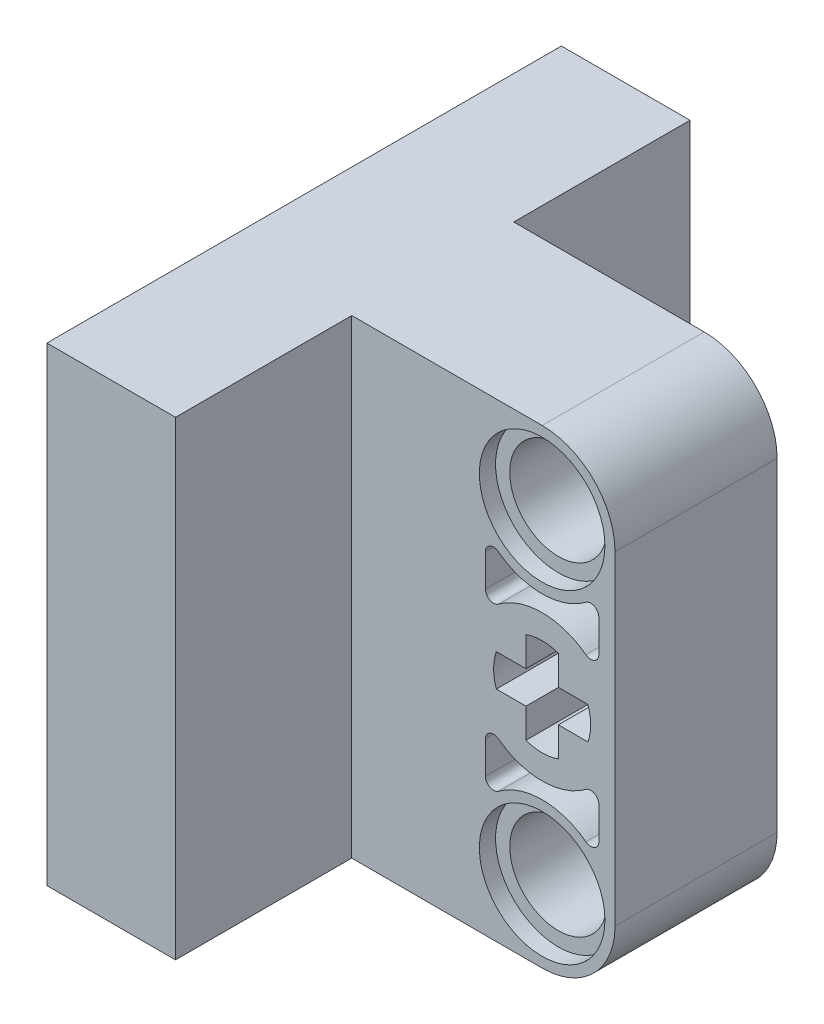
SolidWorks part; units mm, degrees
ref_plane "Front Plane" through (0, 0, 0) normal (0, 0, 1) x (1, 0, 0)
ref_plane "Top Plane" through (0, 0, 0) normal (0, 1, 0) x (1, 0, 0)
ref_plane "Right Plane" through (0, 0, 0) normal (1, 0, 0) x (0, 0, -1)
ref_plane "Plane1" through (0, 0, 4) normal (0, 0, 1) x (1, 0, 0)
sketch "Sketch1" plane through (0, 0, 4) normal (0, 0, 1) x (1, 0, 0)
  line L0 (-3.6, 0) -> (-3.6, -16)
  line L1 (3.6, -16) -> (3.6, 0)
  arc A0 (3.6, 0) -> (-3.6, 0) centre (0, 0) ccw
  arc A1 (-3.6, -16) -> (3.6, -16) centre (0, -16) ccw
  dimension "D1" = 7.2
  dimension "D2" = 16
extrude "Boss-Extrude1" add sketch "Sketch1" against normal blind 8
ref_plane "Plane6" through (0, 0, 0) normal (-1, 0, 0) x (0, 0, 1)
sketch "Sketch15" plane through (0, 0, 0) normal (-1, 0, 0) x (0, 0, 1)
  line L1 (-4, 3.6) -> (4, 3.6)
  line L2 (-4, 3.6) -> (-4, -19.6)
  line L3 (-4, -19.6) -> (4, -19.6)
  line L4 (4, 3.6) -> (4, -19.6)
extrude "Boss-Extrude2" add sketch "Sketch15" along normal blind 15.75
sketch "Sketch3" plane through (0, 0, 4) normal (0, 0, 1) x (1, 0, 0)
  line L0 (2.8, -4.8) -> (2.8, -3.2)
  line L1 (-2.8, -3.2) -> (-2.8, -4.8)
  arc A0 (2.8, -3.2) -> (2.16, -2.88) centre (2.4, -3.2) ccw
  arc A1 (2.16, -2.88) -> (-2.16, -2.88) centre (0, 0) cw
  arc A2 (-2.16, -2.88) -> (-2.8, -3.2) centre (-2.4, -3.2) ccw
  arc A3 (-2.8, -4.8) -> (-2.16, -5.12) centre (-2.4, -4.8) ccw
  arc A4 (-2.16, -5.12) -> (2.16, -5.12) centre (0, -8) cw
  arc A5 (2.16, -5.12) -> (2.8, -4.8) centre (2.4, -4.8) ccw
extrude "Cut-Extrude2" cut sketch "Sketch3" against normal blind 3.1
sketch "Sketch5" plane through (0, 0, 4) normal (0, 0, 1) x (1, 0, 0)
  line L0 (2.8, -12.8) -> (2.8, -11.2)
  line L1 (-2.8, -11.2) -> (-2.8, -12.8)
  arc A0 (2.8, -11.2) -> (2.16, -10.88) centre (2.4, -11.2) ccw
  arc A1 (2.16, -10.88) -> (-2.16, -10.88) centre (0, -8) cw
  arc A2 (-2.16, -10.88) -> (-2.8, -11.2) centre (-2.4, -11.2) ccw
  arc A3 (-2.8, -12.8) -> (-2.16, -13.12) centre (-2.4, -12.8) ccw
  arc A4 (-2.16, -13.12) -> (2.16, -13.12) centre (0, -16) cw
  arc A5 (2.16, -13.12) -> (2.8, -12.8) centre (2.4, -12.8) ccw
extrude "Cut-Extrude4" cut sketch "Sketch5" against normal blind 3.1
sketch "Sketch7" plane through (0, 0, -4) normal (0, 0, -1) x (-1, 0, 0)
  line L0 (2.8, -4.8) -> (2.8, -3.2)
  line L1 (-2.8, -3.2) -> (-2.8, -4.8)
  arc A0 (2.8, -3.2) -> (2.16, -2.88) centre (2.4, -3.2) ccw
  arc A1 (2.16, -2.88) -> (-2.16, -2.88) centre (0, 0) cw
  arc A2 (-2.16, -2.88) -> (-2.8, -3.2) centre (-2.4, -3.2) ccw
  arc A3 (-2.8, -4.8) -> (-2.16, -5.12) centre (-2.4, -4.8) ccw
  arc A4 (-2.16, -5.12) -> (2.16, -5.12) centre (0, -8) cw
  arc A5 (2.16, -5.12) -> (2.8, -4.8) centre (2.4, -4.8) ccw
extrude "Cut-Extrude6" cut sketch "Sketch7" against normal blind 3.1
sketch "Sketch8" plane through (0, 0, -4) normal (0, 0, -1) x (-1, 0, 0)
  line L0 (-2.8, -11.2) -> (-2.8, -12.8)
  line L1 (2.8, -12.8) -> (2.8, -11.2)
  arc A0 (2.16, -10.88) -> (-2.16, -10.88) centre (0, -8) cw
  arc A1 (-2.16, -10.88) -> (-2.8, -11.2) centre (-2.4, -11.2) ccw
  arc A2 (-2.8, -12.8) -> (-2.16, -13.12) centre (-2.4, -12.8) ccw
  arc A3 (-2.16, -13.12) -> (2.16, -13.12) centre (0, -16) cw
  arc A4 (2.16, -13.12) -> (2.8, -12.8) centre (2.4, -12.8) ccw
  arc A5 (2.8, -11.2) -> (2.16, -10.88) centre (2.4, -11.2) ccw
extrude "Cut-Extrude7" cut sketch "Sketch8" against normal blind 3.1
ref_plane "Plane2" through (0, -16, 0) normal (0, 1, 0) x (1, 0, 0)
sketch "Sketch10" plane through (0, -16, 0) normal (0, 1, 0) x (1, 0, 0)
  line L0 (3.1, 4) -> (0, 4)
  line L1 (0, 4) -> (0, -4)
  line L2 (0, -4) -> (3.1, -4)
  line L3 (3.1, -4) -> (3.1, -3.2)
  line L4 (3.1, -3.2) -> (2.4, -3.2)
  line L5 (2.4, -3.2) -> (2.4, 3.2)
  line L6 (2.4, 3.2) -> (3.1, 3.2)
  line L7 (3.1, 3.2) -> (3.1, 4)
  line L8 (0, 4) -> (0, -4) construction
revolve "Cut-Revolve1" cut sketch "Sketch10" angle 360 about L8
ref_plane "Plane3" through (0, 16, 0) normal (0, 1, 0) x (1, 0, 0)
ref_plane "Plane4" through (0, -8, 0) normal (0, 1, 0) x (1, 0, 0)
sketch "Sketch12" plane through (0, -8, 0) normal (0, 1, 0) x (1, 0, 0)
  line L0 (3.1, 4) -> (0, 4)
  line L1 (0, 4) -> (0, -4)
  line L2 (0, -4) -> (3.1, -4)
  line L3 (3.1, -4) -> (3.1, -3.2)
  line L4 (3.1, -3.2) -> (2.4, -3.2)
  line L5 (2.4, -3.2) -> (2.4, 3.2)
  line L6 (2.4, 3.2) -> (3.1, 3.2)
  line L7 (3.1, 3.2) -> (3.1, 4)
  line L8 (0, 4) -> (0, -4) construction
sketch "Sketch13" plane through (0, 0, 0) normal (0, 1, 0) x (1, 0, 0)
  line L0 (3.1, 4) -> (0, 4)
  line L1 (0, 4) -> (0, -4)
  line L2 (0, -4) -> (3.1, -4)
  line L3 (3.1, -4) -> (3.1, -3.2)
  line L4 (3.1, -3.2) -> (2.4, -3.2)
  line L5 (2.4, -3.2) -> (2.4, 3.2)
  line L6 (2.4, 3.2) -> (3.1, 3.2)
  line L7 (3.1, 3.2) -> (3.1, 4)
  line L8 (0, 4) -> (0, -4) construction
revolve "Cut-Revolve4" cut sketch "Sketch13" angle 360 about L8
ref_plane "Plane5" through (0, 8, 0) normal (0, 1, 0) x (1, 0, 0)
sketch "Sketch14" plane through (0, 0, 4) normal (0, 0, 1) x (1, 0, 0)
  line L0 (-3.6, -8) -> (-2.26, -8) construction
  line L2 (-2.26, -8) -> (-2.26, -7.2) construction
  line L3 (-2.26, -8) -> (-2.26, -8.8) construction
  line L4 (-2.26, -7.2) -> (-0.8, -7.2)
  line L5 (-0.8, -7.2) -> (-0.8, -5.74)
  line L6 (-0.8, -5.74) -> (0.8, -5.74) construction
  line L7 (0.8, -5.74) -> (0.8, -7.2)
  line L8 (0.8, -7.2) -> (2.26, -7.2)
  line L9 (2.26, -7.2) -> (2.26, -8.8) construction
  line L10 (2.26, -8.8) -> (0.8, -8.8)
  line L11 (0.8, -8.8) -> (0.8, -10.26)
  line L12 (0.8, -10.26) -> (-0.8, -10.26) construction
  line L13 (-0.8, -10.26) -> (-0.8, -8.8)
  line L14 (-0.8, -8.8) -> (-2.26, -8.8)
  line L16 (3.6, -16) -> (3.6, 0) construction
  line L17 (-15.75, 3.6) -> (0, 3.6) construction
  arc A0 (0.8, -5.74) -> (-0.8, -5.74) centre (0, -8.0027) ccw
  arc A1 (2.26, -7.2) -> (2.26, -8.8) centre (-0.0027, -8) cw
  arc A2 (0.8, -10.26) -> (-0.8, -10.26) centre (0, -7.9973) cw
  arc A3 (-2.26, -8.8) -> (-2.26, -7.2) centre (0.0027, -8) cw
  point P23 (-3.3065, -8)
  dimension "D13" = 2.4
  dimension "D14" = 2.4
  dimension "D15" = 2.4
  dimension "D16" = 2.4
  dimension "D1" = 1.34
  dimension "D2" = 0.8
  dimension "D3" = 0.8
  dimension "D4" = 1.46
  dimension "D5" = 1.46
  dimension "D6" = 1.6
  dimension "D7" = 1.46
  dimension "D8" = 1.46
  dimension "D9" = 1.6
  dimension "D10" = 1.46
  dimension "D11" = 1.46
  dimension "D12" = 1.6
  dimension "D17" = 7.2
  dimension "D18" = 11.6
extrude "Cut-Extrude12" cut sketch "Sketch14" against normal through all contours A3 L14 L13 A2 L11 L10 A1 L8 L7 A0 L5 L4
sketch "Sketch16" plane through (0, 0, 4) normal (0, 0, 1) x (1, 0, 0)
  point P0 (0, 3.6)
  point P1 (0, 3.6)
  point P3 (-0.1507, 3.3132)
  point P5 (0, 0)
ref_plane "Plane7" through (0, 0, 0) normal (0, 0, -1) x (-1, 0, 0)
sketch "Sketch18" plane through (0, 0, 0) normal (0, 0, -1) x (-1, 0, 0)
  line L1 (15.75, 3.6) -> (9.4, 3.6)
  line L2 (15.75, 3.6) -> (15.75, -19.6)
  line L3 (15.75, -19.6) -> (9.4, -19.6)
  line L4 (9.4, 3.6) -> (9.4, -19.6)
  line L5 (15.75, -19.6) -> (0, -19.6) construction
  point P7 (15.3935, 3.2469)
  dimension "D1" = 6.35
extrude "Boss-Extrude3" add sketch "Sketch18" along normal mid plane 25.4
